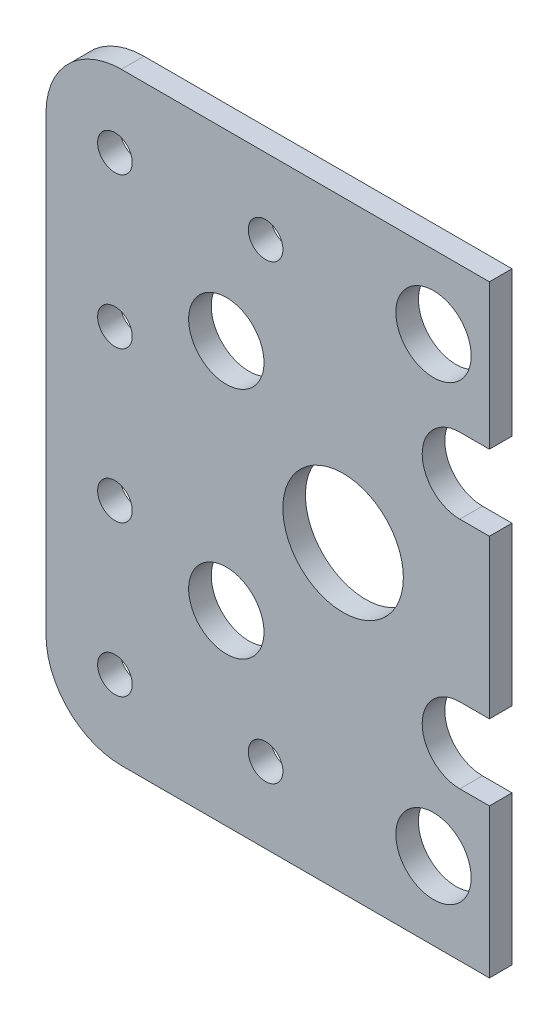
SolidWorks part; units mm, degrees
ref_plane "Front Plane" through (0, 0, 0) normal (0, 0, 1) x (1, 0, 0)
ref_plane "Top Plane" through (0, 0, 0) normal (0, 1, 0) x (1, 0, 0)
ref_plane "Right Plane" through (0, 0, 0) normal (1, 0, 0) x (0, 0, -1)
sketch "Sketch1" plane through (0, 0, 0) normal (0, 0, 1) x (1, 0, 0)
  line L0 (157.9607, -71.8662) -> (165.3807, -71.8662)
  line L1 (116.5258, -71.8662) -> (157.9607, -71.8662)
  line L2 (106.5258, -81.8662) -> (106.5258, -141.8968)
  line L3 (116.5258, -151.8968) -> (157.9607, -151.8968)
  line L4 (165.3807, -71.8662) -> (165.3807, -91.1142)
  line L5 (145.9607, -111.5917) -> (157.9607, -111.5917) construction
  line L6 (157.9607, -111.5917) -> (157.9607, -81.5917) construction
  line L7 (157.9607, -111.5917) -> (157.9607, -141.5917) construction
  line L8 (165.3807, -151.8968) -> (157.9607, -151.8968)
  line L9 (161.4607, -91.1142) -> (165.3807, -91.1142)
  line L10 (161.4607, -101.1142) -> (165.3807, -101.1142)
  line L11 (161.4607, -122.1142) -> (165.3807, -122.1142)
  line L12 (161.4607, -132.1142) -> (165.3807, -132.1142)
  line L13 (165.3807, -101.1142) -> (165.3807, -122.1142)
  line L14 (165.3807, -132.1142) -> (165.3807, -151.8968)
  circle A0 centre (115.6746, -101.8662) radius 2.3
  circle A1 centre (115.6746, -121.8662) radius 2.3
  circle A2 centre (135.6746, -141.8662) radius 2.3
  circle A3 centre (135.6746, -81.8662) radius 2.3
  circle A4 centre (115.6746, -81.8662) radius 2.3
  circle A5 centre (115.6746, -141.8662) radius 2.3
  arc A6 (161.4607, -91.1142) -> (161.4607, -101.1142) centre (161.4607, -96.1142) ccw
  arc A7 (161.4607, -122.1142) -> (161.4607, -132.1142) centre (161.4607, -127.1142) ccw
  circle A9 centre (130.4607, -96.1142) radius 5
  circle A10 centre (145.9607, -111.5917) radius 8
  circle A11 centre (130.4607, -127.1142) radius 5
  arc A13 (106.5258, -141.8968) -> (116.5258, -151.8968) centre (116.5258, -141.8968) ccw
  arc A14 (116.5258, -71.8662) -> (106.5258, -81.8662) centre (116.5258, -81.8662) ccw
  circle A15 centre (157.9607, -81.5917) radius 5
  circle A16 centre (157.9607, -141.5917) radius 5
  point P47 (106.5258, -71.8662)
  dimension "D4" = 12
  dimension "D2" = 30
  dimension "D3" = 30
extrude "Boss-Extrude1" add sketch "Sketch1" along normal blind 3
